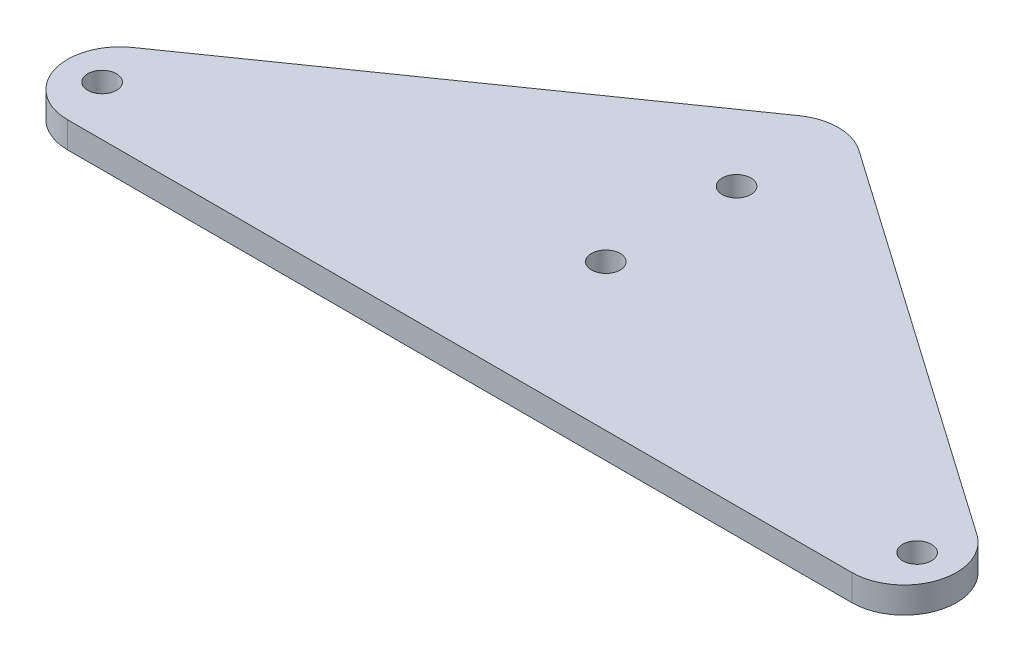
SolidWorks part; units mm, degrees
material "1060 Alloy"
ref_plane "Front Plane" through (0, 0, 0) normal (0, 0, 1) x (1, 0, 0)
ref_plane "Top Plane" through (0, 0, 0) normal (0, 1, 0) x (1, 0, 0)
ref_plane "Right Plane" through (0, 0, 0) normal (1, 0, 0) x (0, 0, -1)
sketch "Sketch2" plane through (0, 0, 0) normal (0, 1, 0) x (1, 0, 0)
  line L0 (-5.7286, 62.6639) -> (-80.7286, 10.2458)
  line L1 (-75, -7.9507) -> (75, -7.9507)
  line L2 (80.7286, 10.2458) -> (5.7286, 62.6639)
  line L3 (0, 66.6677) -> (0, -7.9507) construction
  arc A0 (75, -7.9507) -> (80.7286, 10.2458) centre (75, 2.0493) ccw
  arc A1 (-80.7286, 10.2458) -> (-75, -7.9507) centre (-75, 2.0493) ccw
  arc A2 (-5.7286, 62.6639) -> (5.7286, 62.6639) centre (0, 54.4674) cw
  point P2 (0, 46.6677)
  point P6 (0, 26.6677)
  point P8 (106.7643, -7.9507)
  point P11 (-106.7643, -7.9507)
  dimension "D5" = 10
  dimension "D2" = 20
  dimension "D3" = 20
  dimension "D4" = 34.95
  dimension "D1" = 150
extrude "Boss-Extrude1" add sketch "Sketch2" along normal blind 5
hole_wizard "M5 Clearance Hole1" positions "Sketch3" profile "Sketch4" hole size "M5" standard "AS" end condition through all
sketch "Sketch3" plane through (0, 5, 0) normal (0, 1, 0) x (1, 0, 0)
  point P0 (0, 45)
  point P3 (0, 20)
  dimension "D1" = 25
  dimension "D2" = 20
sketch "Sketch4" plane through (0, 5, -45) normal (1, 0, 0) x (0, 0, 1)
  line L0 (0, 0) -> (0, 5)
  line L1 (0, 5) -> (2.75, 5)
  line L2 (2.75, 5) -> (2.75, 0)
  line L5 (2.75, 0) -> (0, 0)
  line L11 (0, -6.35) -> (0, 107.95) construction
  dimension "Thru Hole Dia." = 5.5
  dimension "Thru Hole Depth" = 5
sketch "Sketch5" plane through (0, 5, 0) normal (0, 1, 0) x (1, 0, 0)
  line L0 (-83.8714, -2.5657) -> (-77.9289, 1.5875) construction
  line L1 (-77.9289, 1.5875) -> (-77.9289, -7.5122) construction
  line L2 (-5.7286, 62.6639) -> (-80.7286, 10.2458) construction
  line L3 (-77.9289, 1.5875) -> (-80.7286, 10.2458) construction
  arc A1 (-80.7286, 10.2458) -> (-75, -7.9507) centre (-75, 2.0493) ccw construction
  dimension "D1" = 7.25
hole_wizard "M5 Clearance Hole2" positions "Sketch6" profile "Sketch7" hole size "M5" standard "AS" end condition through all
sketch "Sketch6" plane through (0, 5, 0) normal (0, 1, 0) x (1, 0, 0)
  point P0 (-77.9289, 1.5875)
sketch "Sketch7" plane through (-77.9289, 5, -1.5875) normal (1, 0, 0) x (0, 0, 1)
  line L0 (0, 0) -> (0, 5)
  line L1 (0, 5) -> (2.75, 5)
  line L2 (2.75, 5) -> (2.75, 0)
  line L5 (2.75, 0) -> (0, 0)
  line L11 (0, -6.35) -> (0, 107.95) construction
  dimension "Thru Hole Dia." = 5.5
  dimension "Thru Hole Depth" = 5
mirror "Mirror1" about plane through (0, 0, 0) normal (1, 0, 0) of "M5 Clearance Hole2"
equation "\"keelOutDiameter\"= 1in"
equation "\"keelInDiameter\"= \"keelOutDiameter\" - 0.125in"
equation "\"frontBoltClearance\"= 7.25mm"
equation "\"betweenBoltsDistance\"= 20mm"
equation "\"D2@Sketch2\"=\"betweenBoltsDistance\""
equation "\"plateThickness\"= 5mm"
equation "\"D1@Boss-Extrude1\"=\"plateThickness\""
equation "\"D1@Sketch5\"=\"frontBoltClearance\""
